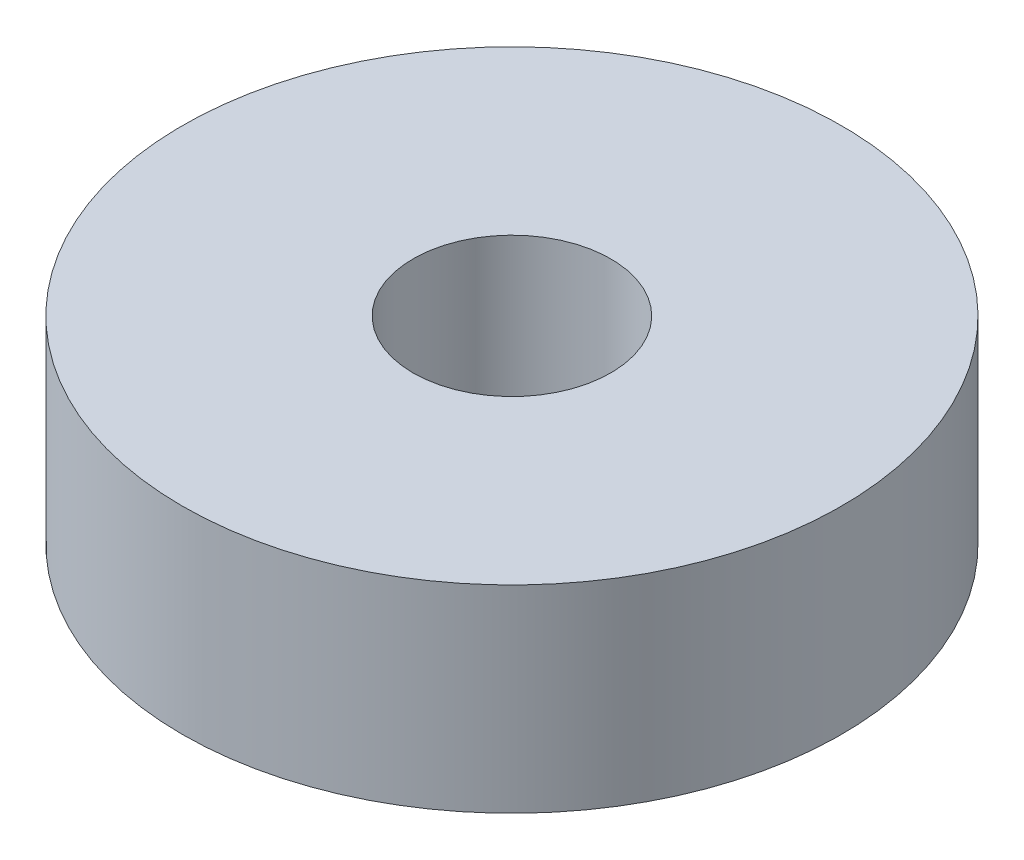
SolidWorks part; units mm, degrees
ref_plane "Front Plane" through (0, 0, 0) normal (0, 0, 1) x (1, 0, 0)
ref_plane "Top Plane" through (0, 0, 0) normal (0, 1, 0) x (1, 0, 0)
ref_plane "Right Plane" through (0, 0, 0) normal (1, 0, 0) x (0, 0, -1)
sketch "Sketch1" plane through (0, 0, 0) normal (0, 1, 0) x (1, 0, 0)
  circle A0 centre (0, 0) radius 5
  dimension "D1" = 10
extrude "Boss-Extrude1" add sketch "Sketch1" along normal blind 3
hole_wizard "Ø3.0mm Dowel Hole1" positions "Sketch2" profile "Sketch3" hole size "Ø3.0" standard "ISO" end condition through all
sketch "Sketch2" plane through (0, 3, 0) normal (0, 1, 0) x (1, 0, 0)
  point P0 (0, 0)
sketch "Sketch3" plane through (0, 3, 0) normal (1, 0, 0) x (0, 0, 1)
  line L0 (0, 0) -> (0, 3)
  line L1 (0, 3) -> (1.5, 3)
  line L2 (1.5, 3) -> (1.5, 0)
  line L5 (1.5, 0) -> (0, 0)
  line L11 (0, -6.35) -> (0, 107.95) construction
  dimension "Thru Hole Dia." = 3
  dimension "Thru Hole Depth" = 3
